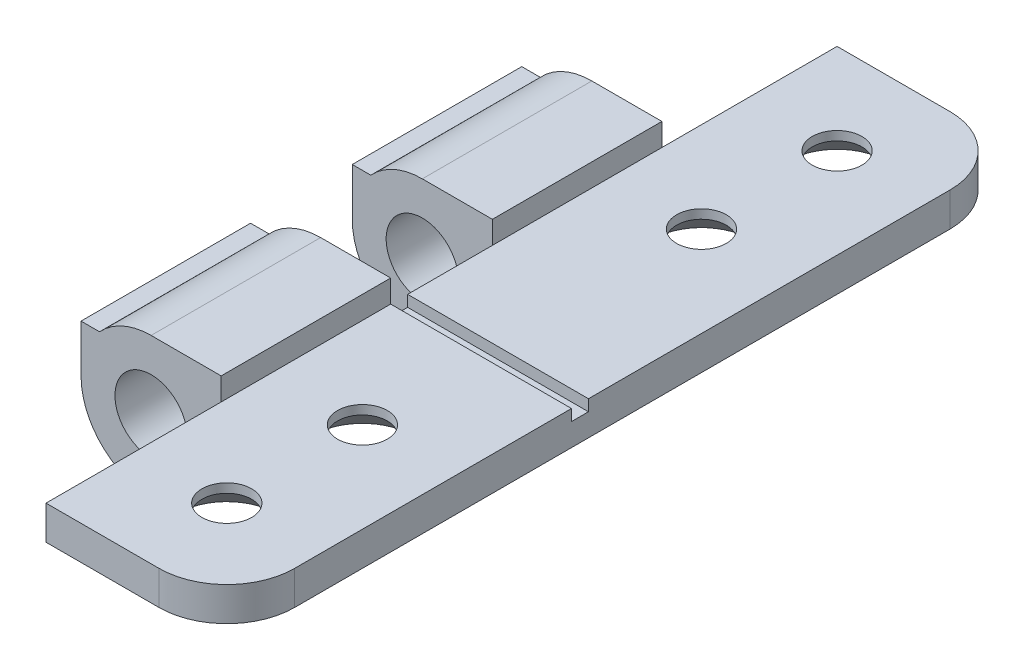
SolidWorks part; units mm, degrees
material "6063-T6"
ref_plane "Front Plane" through (0, 0, 0) normal (0, 0, 1) x (1, 0, 0)
ref_plane "Top Plane" through (0, 0, 0) normal (0, 1, 0) x (1, 0, 0)
ref_plane "Right Plane" through (0, 0, 0) normal (1, 0, 0) x (0, 0, -1)
sketch "Sketch2" plane through (0, 0, 0) normal (0, 0, 1) x (1, 0, 0)
  line L0 (3.1, 2.1) -> (11.1, 2.1)
  line L1 (11.1, 2.1) -> (11.1, 0.6)
  line L2 (11.1, 0.6) -> (3.1, 0.6)
  line L3 (0, 1.6) -> (15.0271, 1.6) construction
  line L4 (3.1, 2.1) -> (3.1, 3.1)
  line L5 (3.1, 3.1) -> (0, 3.1)
  line L6 (3.1, 0) -> (3.1, 0.6)
  line L7 (-3.1, 0) -> (-3.1, 2.1)
  line L8 (-3.1, 2.1) -> (-2.2804, 2.1)
  circle A0 centre (0, 0) radius 1.6
  arc A1 (0, 3.1) -> (-2.2804, 2.1) centre (0, 0) ccw
  arc A2 (-3.1, 0) -> (3.1, 0) centre (0, 0) ccw
  dimension "D1" = 3.2
  dimension "D2" = 1.5
  dimension "D3" = 1.5
  dimension "D4" = 8
  dimension "D5" = 0.5
extrude "Boss-Extrude1" add sketch "Sketch2" along normal blind 7.5
sketch "Sketch4" plane through (0, 0, 7.5) normal (0, 0, 1) x (1, 0, 0)
  line L1 (11.1, 2.1) -> (3.1, 2.1)
  line L2 (11.1, 2.1) -> (11.1, 0.6)
  line L3 (11.1, 0.6) -> (3.1, 0.6)
  line L4 (3.1, 2.1) -> (3.1, 0.6)
  line L5 (11.1, 2.1) -> (3.1, 0.6) construction
  line L6 (11.1, 0.6) -> (3.1, 2.1) construction
  point P4 (7.1, 1.35)
extrude "Boss-Extrude3" add sketch "Sketch4" along normal blind 4.5
sketch "Sketch5" plane through (0, 0, 12) normal (0, 0, 1) x (1, 0, 0)
  line L0 (11.1, 0.6) -> (11.1, 2.1) construction
  line L1 (11.1, 2.1) -> (3.1, 2.1) construction
  line L2 (-3.1, 2.1) -> (-3.1, 0) construction
  line L3 (3.1, 0.6) -> (11.1, 0.6) construction
  line L4 (-2.2804, 2.1) -> (-3.1, 2.1) construction
  line L5 (3.1, 2.1) -> (3.1, 3.1) construction
  line L6 (3.1, 3.1) -> (0, 3.1) construction
  line L7 (3.1, 0) -> (3.1, 0.6) construction
  line L8 (11.1, 0.6) -> (11.1, 2.1)
  line L9 (11.1, 2.1) -> (3.1, 2.1)
  line L11 (3.1, 0.6) -> (11.1, 0.6)
  line L13 (3.1, 2.1) -> (3.1, 3.1)
  line L14 (3.1, 3.1) -> (0, 3.1)
  line L15 (3.1, 0) -> (3.1, 0.6)
  line L16 (-3.1, 2.1) -> (-3.1, 0)
  line L17 (-2.2804, 2.1) -> (-3.1, 2.1)
  circle A1 centre (0, 0) radius 1.6 construction
  circle A3 centre (0, 0) radius 1.6
  arc A4 (-3.1, 0) -> (3.1, 0) centre (0, 0) ccw construction
  arc A5 (0, 3.1) -> (-2.2804, 2.1) centre (0, 0) ccw construction
  arc A6 (-3.1, 0) -> (3.1, 0) centre (0, 0) ccw
  arc A7 (0, 3.1) -> (-2.2804, 2.1) centre (0, 0) ccw
extrude "Boss-Extrude4" add sketch "Sketch5" along normal blind 7.5
sketch "Sketch6" plane through (0, 0, 19.5) normal (0, 0, 1) x (1, 0, 0)
  line L1 (11.1, 0.6) -> (3.1, 0.6)
  line L2 (11.1, 0.6) -> (11.1, 2.1)
  line L3 (11.1, 2.1) -> (3.1, 2.1)
  line L4 (3.1, 0.6) -> (3.1, 2.1)
  line L5 (11.1, 0.6) -> (3.1, 2.1) construction
  line L6 (11.1, 2.1) -> (3.1, 0.6) construction
  point P4 (7.1, 1.35)
extrude "Boss-Extrude5" add sketch "Sketch6" along normal blind 7.75
sketch "Sketch7" plane through (0, 0, 0) normal (0, 0, -1) x (-1, 0, 0)
  line L4 (-11.1, 2.1) -> (-11.1, 0.6)
  line L5 (-3.1, 2.1) -> (-11.1, 2.1)
  line L6 (-3.1, 0.6) -> (-3.1, 2.1)
  line L7 (-11.1, 0.6) -> (-3.1, 0.6)
  line L8 (-11.1, 2.1) -> (-11.1, 0.6)
  line L9 (-3.1, 2.1) -> (-11.1, 2.1)
  line L10 (-3.1, 0.6) -> (-3.1, 2.1)
  line L11 (-11.1, 0.6) -> (-3.1, 0.6)
  dimension "D1" = 0
extrude "Boss-Extrude6" add sketch "Sketch7" along normal blind 7.75
sketch "Sketch8" plane through (3.1, 0, 0) normal (-1, 0, 0) x (0, 0, 1)
  line L5 (12, 2.1) -> (11.25, 2.1)
  line L6 (12, 2.1) -> (12, 1.6)
  line L7 (12, 1.6) -> (11.25, 1.6)
  line L8 (11.25, 2.1) -> (11.25, 1.6)
  line L9 (12, 2.1) -> (11.25, 1.6) construction
  line L10 (12, 1.6) -> (11.25, 2.1) construction
  point P4 (11.625, 1.85)
  dimension "D1" = 0.5
  dimension "D2" = 0.75
extrude "Cut-Extrude1" cut sketch "Sketch8" against normal through all
sketch "Sketch9" plane through (0, 0.6, 0) normal (0, -1, 0) x (1, 0, 0)
  line L0 (7.1, 27.25) -> (7.1, -7.75) construction
  line L1 (3.1, 27.25) -> (11.1, 27.25) construction
  line L2 (11.1, -7.75) -> (3.1, -7.75) construction
  line L3 (7.1, -7.75) -> (11.1, -7.75) construction
  line L4 (11.1, -7.75) -> (11.1, 27.25) construction
  circle A0 centre (7.1, 23.25) radius 1.1
  circle A1 centre (7.1, 17.25) radius 1.1
  circle A2 centre (7.1, 2.25) radius 1.1
  circle A3 centre (7.1, -3.75) radius 1.1
  dimension "D6" = 2.2
  dimension "D1" = 35
  dimension "D2" = 15
  dimension "D3" = 6
  dimension "D4" = 6
  dimension "D5" = 10
extrude "Cut-Extrude2" cut sketch "Sketch9" against normal through all
chamfer "Chamfer1" distance 1.1 angle 45 4 edges at (8.2, 0.6, -3.75) (8.2, 0.6, 2.25) (8.2, 0.6, 23.25) (8.2, 0.6, 17.25)
fillet "Fillet1" radius 3 2 edges at (11.1, 1.35, 27.25) (11.1, 1.35, -7.75)
equation "\"D4@Sketch9\"=\"D3@Sketch9\""
equation "\"D5@Sketch9\"=(\"D1@Sketch9\"-\"D2@Sketch9\")/2"
